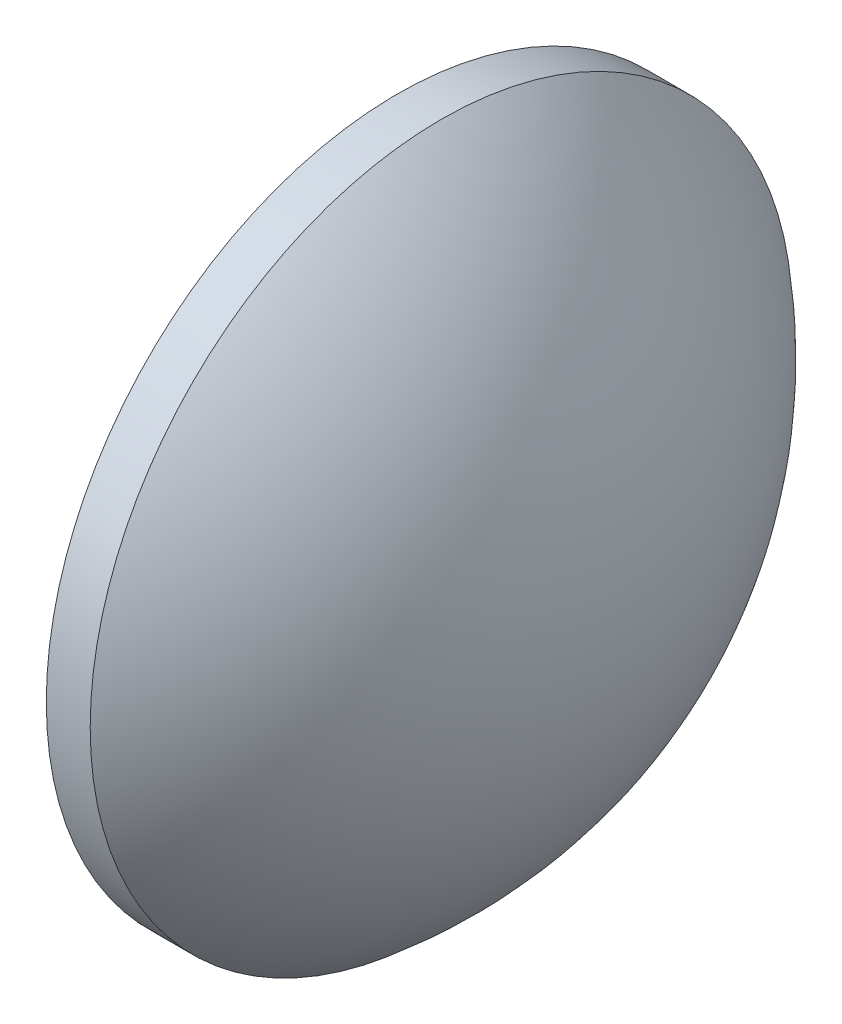
SolidWorks part; units mm, degrees
ref_plane "前视基准面" through (0, 0, 0) normal (0, 0, 1) x (1, 0, 0)
ref_plane "上视基准面" through (0, 0, 0) normal (0, 1, 0) x (1, 0, 0)
ref_plane "右视基准面" through (0, 0, 0) normal (1, 0, 0) x (0, 0, -1)
sketch "草图1" plane through (0, 0, 0) normal (0, 0, 1) x (1, 0, 0)
  line L0 (108.6656, 65.0209) -> (127.8417, 65.0209) construction
  line L1 (113.3601, 65.0209) -> (113.3601, 85.0209)
  line L2 (125.3401, 65.0209) -> (113.3601, 65.0209)
  line L5 (115.8601, 85.0209) -> (113.3601, 85.0209)
  arc A0 (125.3401, 65.0209) -> (115.8601, 85.0209) centre (99.5031, 65.0209) ccw
revolve "旋转1" add sketch "草图1" angle 360 about L0
